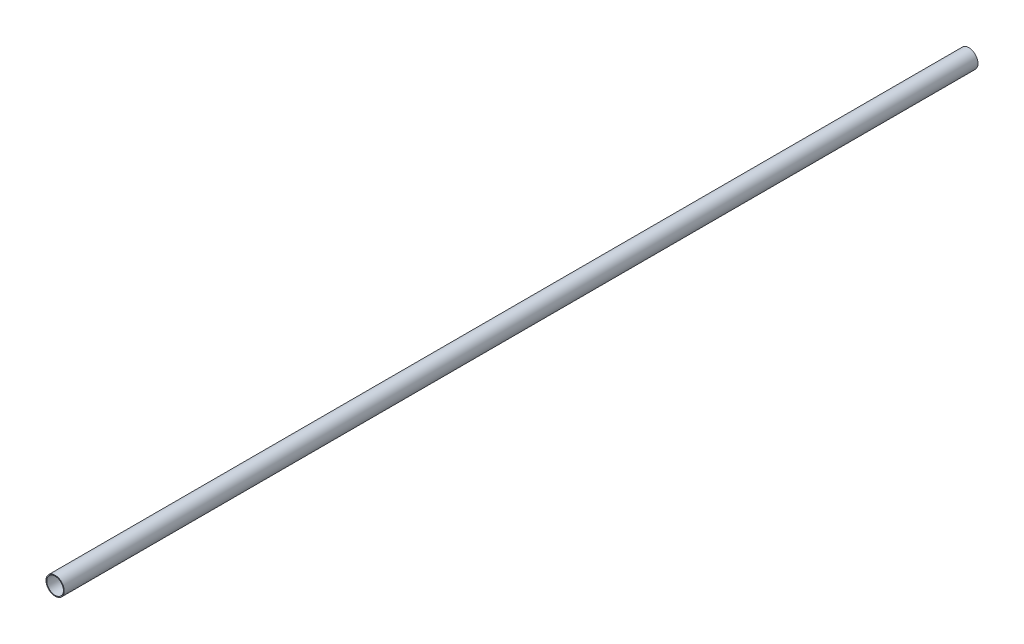
SolidWorks part; units mm, degrees
material "Hexcel AS4C (3000 Filaments)"
ref_plane "Front Plane" through (0, 0, 0) normal (0, 0, 1) x (1, 0, 0)
ref_plane "Top Plane" through (0, 0, 0) normal (0, 1, 0) x (1, 0, 0)
ref_plane "Right Plane" through (0, 0, 0) normal (1, 0, 0) x (0, 0, -1)
sketch "Sketch1" plane through (0, 0, 0) normal (0, 0, 1) x (1, 0, 0)
  circle A0 centre (0, 0) radius 10
  circle A1 centre (0, 0) radius 11
  dimension "D1" = 22
  dimension "D2" = 20
extrude "Boss-Extrude1" add sketch "Sketch1" along normal blind 1100
